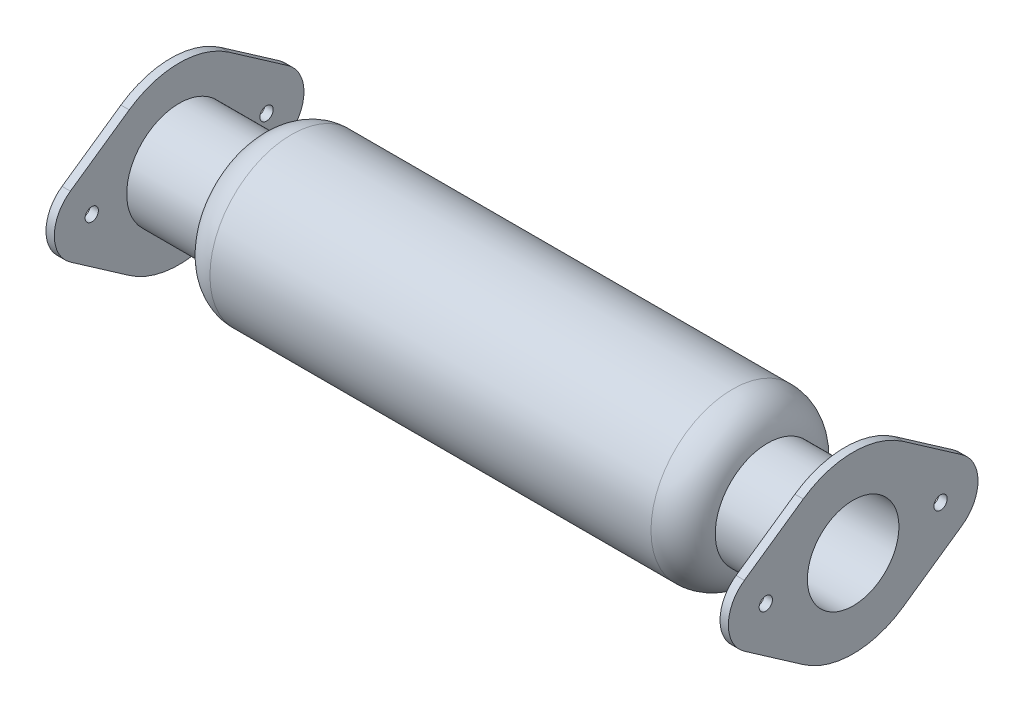
SolidWorks part; units mm, degrees
ref_plane "Front Plane" through (0, 0, 0) normal (0, 0, 1) x (1, 0, 0)
ref_plane "Top Plane" through (0, 0, 0) normal (0, 1, 0) x (1, 0, 0)
ref_plane "Right Plane" through (0, 0, 0) normal (1, 0, 0) x (0, 0, -1)
sketch "Sketch1" plane through (0, 0, 0) normal (0, 1, 0) x (1, 0, 0)
  line L0 (0, 0) -> (0, 59459.7927) construction
  line L1 (0, 0) -> (-59459.7927, 0) construction
  line L2 (-200, 27.5) -> (-150, 27.5)
  line L3 (-132.5, 45) -> (132.5, 45)
  line L4 (150, 27.5) -> (200, 27.5)
  line L5 (-200, 31.5) -> (-153.6246, 31.5)
  line L6 (-132.5, 49) -> (132.5, 49)
  line L7 (153.6246, 31.5) -> (200, 31.5)
  line L8 (-200, 31.5) -> (-200, 27.5)
  line L9 (200, 31.5) -> (200, 27.5)
  arc A0 (-150, 27.5) -> (-132.5, 45) centre (-132.5, 27.5) cw
  arc A1 (132.5, 45) -> (150, 27.5) centre (132.5, 27.5) cw
  arc A2 (-153.6246, 31.5) -> (-132.5, 49) centre (-132.5, 27.5) cw
  arc A3 (132.5, 49) -> (153.6246, 31.5) centre (132.5, 27.5) cw
  dimension "D1" = 300
  dimension "D2" = 50
  dimension "D3" = 45
  dimension "D4" = 27.5
  dimension "D5" = 4
revolve "Revolve1" add sketch "Sketch1" angle 360 about L1
sketch "Sketch2" plane through (-200, 0, 0) normal (-1, 0, 0) x (0, 0, 1)
  line L0 (-30, 43.0842) -> (-65.3571, 18.4647)
  line L1 (65.3571, 18.4647) -> (30, 43.0842)
  line L2 (65.3571, -18.4647) -> (30, -43.0842)
  line L3 (-65.3571, -18.4647) -> (-30, -43.0842)
  circle A0 centre (0, 0) radius 27.5 construction
  arc A1 (-30, -43.0842) -> (30, -43.0842) centre (0, 0) ccw
  circle A3 centre (0, 0) radius 27.5
  arc A4 (65.3571, -18.4647) -> (65.3571, 18.4647) centre (52.5, 0) ccw
  arc A5 (-65.3571, 18.4647) -> (-65.3571, -18.4647) centre (-52.5, 0) ccw
  arc A6 (30, 43.0842) -> (-30, 43.0842) centre (0, 0) ccw
  circle A7 centre (-52.5, 0) radius 4
  circle A8 centre (52.5, 0) radius 4
  dimension "D1" = 45
  dimension "D2" = 105
  dimension "D3" = 8
extrude "Boss-Extrude1" add sketch "Sketch2" along normal blind 5
mirror "Mirror1" about plane through (0, 0, 0) normal (1, 0, 0) of "Boss-Extrude1"
